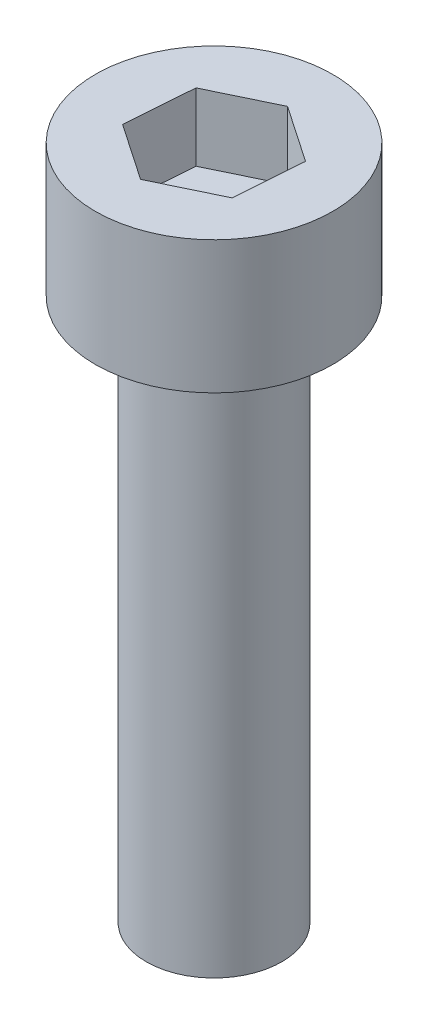
SolidWorks part; units mm, degrees
ref_plane "前视基准面" through (0, 0, 0) normal (0, 0, 1) x (1, 0, 0)
ref_plane "上视基准面" through (0, 0, 0) normal (0, 1, 0) x (1, 0, 0)
ref_plane "右视基准面" through (0, 0, 0) normal (1, 0, 0) x (0, 0, -1)
sketch "草图1" plane through (0, 0, 0) normal (0, 1, 0) x (1, 0, 0)
  circle A0 centre (0, 0) radius 2
  dimension "D1" = 4
extrude "凸台-拉伸1" add sketch "草图1" along normal blind 16
sketch "草图2" plane through (0, 16, 0) normal (0, 1, 0) x (1, 0, 0)
  circle A0 centre (0, 0) radius 3.5
  dimension "D1" = 7
extrude "凸台-拉伸2" add sketch "草图2" along normal blind 3.91
sketch "草图3" plane through (0, 19.91, 0) normal (0, 1, 0) x (1, 0, 0)
  line L1 (1.6694, -1.1386) -> (1.8208, 0.8764)
  line L2 (1.8208, 0.8764) -> (0.1514, 2.015)
  line L3 (0.1514, 2.015) -> (-1.6694, 1.1386)
  line L4 (-1.6694, 1.1386) -> (-1.8208, -0.8764)
  line L5 (-1.8208, -0.8764) -> (-0.1514, -2.015)
  line L6 (-0.1514, -2.015) -> (1.6694, -1.1386)
  circle A0 centre (0, 0) radius 1.75 construction
  dimension "D1" = 3.5
extrude "切除-拉伸1" cut sketch "草图3" against normal blind 2
